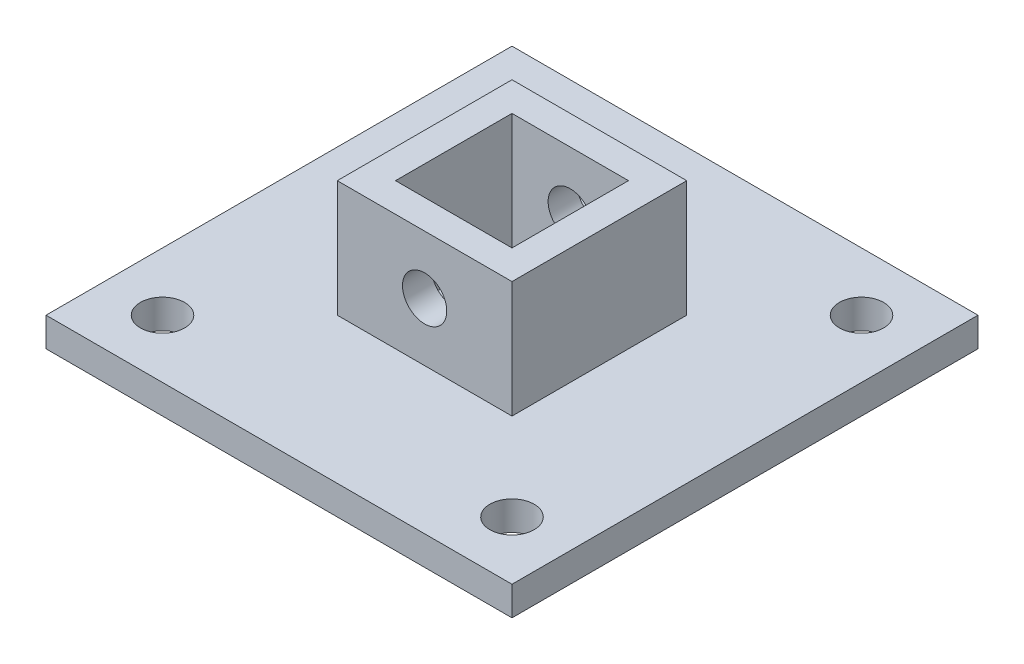
SolidWorks part; units mm, degrees
ref_plane "Front Plane" through (0, 0, 0) normal (0, 0, 1) x (1, 0, 0)
ref_plane "Top Plane" through (0, 0, 0) normal (0, 1, 0) x (1, 0, 0)
ref_plane "Right Plane" through (0, 0, 0) normal (1, 0, 0) x (0, 0, -1)
sketch "Sketch1" plane through (0, 0, 0) normal (0, 1, 0) x (1, 0, 0)
  line L1 (50.8, -50.8) -> (-50.8, -50.8)
  line L2 (50.8, -50.8) -> (50.8, 50.8)
  line L3 (50.8, 50.8) -> (-50.8, 50.8)
  line L4 (-50.8, -50.8) -> (-50.8, 50.8)
  line L5 (50.8, -50.8) -> (-50.8, 50.8) construction
  line L6 (50.8, 50.8) -> (-50.8, -50.8) construction
  point P0 (0, 0)
  dimension "D1" = 101.6
  dimension "D2" = 101.6
extrude "Boss-Extrude1" add sketch "Sketch1" along normal blind 6.35
sketch "Sketch2" plane through (0, 6.35, 0) normal (0, 1, 0) x (1, 0, 0)
  line L1 (-19.05, -19.05) -> (19.05, -19.05)
  line L2 (-19.05, -19.05) -> (-19.05, 19.05)
  line L3 (-19.05, 19.05) -> (19.05, 19.05)
  line L4 (19.05, -19.05) -> (19.05, 19.05)
  line L5 (-19.05, -19.05) -> (19.05, 19.05) construction
  line L6 (-19.05, 19.05) -> (19.05, -19.05) construction
  line L7 (12.7, -12.7) -> (-12.7, -12.7)
  line L8 (12.7, -12.7) -> (12.7, 12.7)
  line L9 (12.7, 12.7) -> (-12.7, 12.7)
  line L10 (-12.7, -12.7) -> (-12.7, 12.7)
  line L11 (12.7, -12.7) -> (-12.7, 12.7) construction
  line L12 (12.7, 12.7) -> (-12.7, -12.7) construction
  point P0 (0, 0)
  point P6 (0, 0)
  dimension "D1" = 38.1
  dimension "D2" = 38.1
  dimension "D3" = 25.4
  dimension "D4" = 25.4
extrude "Boss-Extrude2" add sketch "Sketch2" along normal blind 25.4
sketch "Sketch3" plane through (0, 0, 19.05) normal (0, 0, 1) x (1, 0, 0)
  line L0 (-19.05, 31.75) -> (-19.05, 6.35) construction
  line L1 (-19.05, 31.75) -> (19.05, 31.75) construction
  circle A0 centre (0, 19.05) radius 4.826
  dimension "D3" = 9.652
  dimension "D1" = 19.05
  dimension "D2" = 12.7
extrude "Cut-Extrude1" cut sketch "Sketch3" against normal through all both and the other way through all
sketch "Sketch4" plane through (0, 6.35, 0) normal (0, 1, 0) x (1, 0, 0)
  line L0 (-50.8, 50.8) -> (-50.8, -50.8) construction
  line L1 (-50.8, -50.8) -> (50.8, -50.8) construction
  line L2 (50.8, -50.8) -> (50.8, 50.8) construction
  line L3 (50.8, 50.8) -> (-50.8, 50.8) construction
  circle A0 centre (-38.1, 38.1) radius 4.826
  circle A1 centre (38.1, 38.1) radius 4.826
  circle A2 centre (38.1, -38.1) radius 4.826
  circle A3 centre (-38.1, -38.1) radius 4.826
  point P12 (0, 0)
  point P13 (0, 0)
  point P14 (0, 0)
  point P15 (0, 0)
  point P16 (0, 0)
  point P17 (0, 0)
  dimension "D2" = 9.652
  dimension "D4" = 9.652
  dimension "D6" = 9.652
  dimension "D8" = 9.652
  dimension "D1" = 12.7
  dimension "D3" = 12.7
  dimension "D5" = 12.7
  dimension "D7" = 12.7
extrude "Cut-Extrude2" cut sketch "Sketch4" against normal blind 25.4
